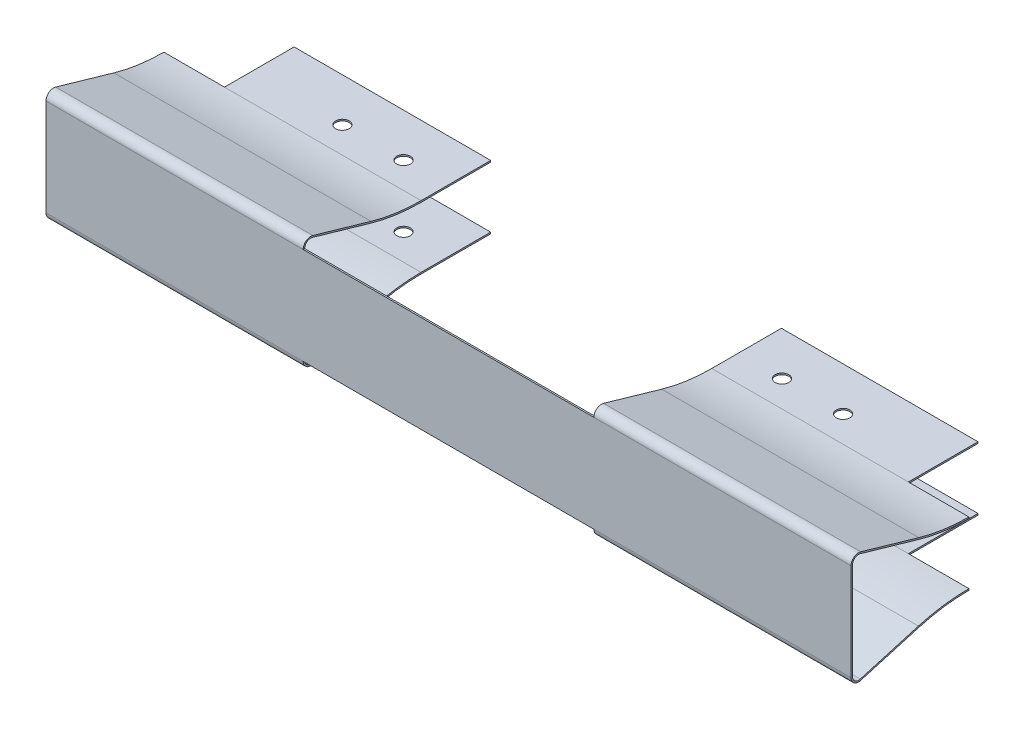
SolidWorks part; units mm, degrees
ref_plane "Front Plane" through (0, 0, 0) normal (0, 0, 1) x (1, 0, 0)
ref_plane "Top Plane" through (0, 0, 0) normal (0, 1, 0) x (1, 0, 0)
ref_plane "Right Plane" through (0, 0, 0) normal (1, 0, 0) x (0, 0, -1)
sketch "Sketch1" plane through (0, 0, 0) normal (1, 0, 0) x (0, 0, -1)
  line L0 (-14.97, 5) -> (-22.97, 5) construction
  line L1 (-24.97, 8) -> (-22.97, 8) construction
  line L2 (-24.97, 8) -> (-24.97, -8) construction
  line L3 (-24.97, -8) -> (-22.97, -8) construction
  line L4 (-14.97, 5) -> (-14.97, 3) construction
  line L5 (-24.97, 8) -> (-14.97, -5) construction
  line L6 (-24.97, -8) -> (-14.97, 5) construction
  line L7 (-22.97, 5) -> (-22.97, 8) construction
  line L8 (-14.97, 3) -> (-21.97, 3) construction
  line L9 (-21.97, 3) -> (-21.97, -3) construction
  line L10 (-21.97, -3) -> (-14.97, -3) construction
  line L11 (-14.97, -5) -> (-22.97, -5) construction
  line L12 (-22.97, -5) -> (-22.97, -8) construction
  line L13 (-14.97, -3) -> (-14.97, -5) construction
  line L14 (-24.97, 8) -> (-24.97, -8)
  line L15 (-14.0876, 6.1819) -> (-23.6921, 8.9606)
  line L16 (-5.75, 5) -> (-5.75, -5) construction
  line L17 (-5.75, -5) -> (5.75, -5) construction
  line L18 (5.75, 5) -> (5.75, -5) construction
  line L19 (-5.75, 5) -> (5.75, -5) construction
  line L20 (-5.75, -5) -> (5.75, 5) construction
  line L21 (-5.75, 5) -> (5.75, 5) construction
  line L22 (-5.75, -5.25) -> (5.75, -5.25)
  line L23 (-5.75, 5) -> (5.75, 5) construction
  line L24 (-14.0181, -6.422) -> (-23.6226, -9.2008)
  line L25 (-14.0876, -6.1819) -> (-23.6921, -8.9606)
  line L26 (-5.75, -5) -> (5.75, -5)
  line L27 (-25.22, 8) -> (-25.22, -8)
  line L28 (-5.75, 5) -> (5.75, 5)
  line L29 (-14.0181, 6.422) -> (-23.6226, 9.2008)
  line L30 (-5.75, 5.25) -> (5.75, 5.25)
  line L31 (5.75, 5.25) -> (5.75, 5)
  line L32 (5.75, -5) -> (5.75, -5.25)
  arc A0 (-24.97, -8) -> (-23.6921, -8.9606) centre (-23.97, -8) ccw
  arc A1 (-23.6921, 8.9606) -> (-24.97, 8) centre (-23.97, 8) ccw
  arc A2 (-5.75, -5.25) -> (-14.0181, -6.422) centre (-5.75, -35) ccw
  arc A3 (-25.22, -8) -> (-23.6226, -9.2008) centre (-23.97, -8) ccw
  arc A4 (-23.6226, 9.2008) -> (-25.22, 8) centre (-23.97, 8) ccw
  arc A5 (-5.75, 5.25) -> (-14.0181, 6.422) centre (-5.75, 35) cw
  arc A6 (-5.75, -5) -> (-14.0876, -6.1819) centre (-5.75, -35) ccw
  arc A7 (-5.75, 5) -> (-14.0876, 6.1819) centre (-5.75, 35) cw
  point P0 (-18.8162, 0)
  point P1 (0, 0)
  dimension "D13" = 30
  dimension "D17" = 1
  dimension "D1" = 16
  dimension "D2" = 10
  dimension "D3" = 2
  dimension "D4" = 2
  dimension "D5" = 2
  dimension "D6" = 3
  dimension "D7" = 6
  dimension "D8" = 3
  dimension "D9" = 11.5
  dimension "D10" = 10
  dimension "D11" = 16.22
  dimension "D12" = 0.25
extrude "Extrude1" add sketch "Sketch1" along normal mid plane 132.92
sketch "Sketch2" plane through (0, 0, 0) normal (0, 0, 1) x (1, 0, 0)
  line L0 (-24, 8) -> (-24, 9.25)
  line L1 (-24, 8) -> (24, 8)
  line L2 (-24, 8) -> (-24, -8) construction
  line L3 (-24, -8) -> (24, -8)
  line L4 (24, 8) -> (24, -8) construction
  line L5 (-24, 8) -> (24, -8) construction
  line L6 (-24, -8) -> (24, 8) construction
  line L8 (-24, 9.25) -> (24, 9.25)
  line L9 (24, 9.25) -> (24, 8)
  line L10 (24, -8) -> (24, -9.25)
  line L12 (24, -9.25) -> (-24, -9.25)
  line L13 (-24, -9.25) -> (-24, -8)
  line L14 (66.46, 9.25) -> (-66.46, 9.25) construction
  line L15 (-66.46, -9.25) -> (66.46, -9.25) construction
  point P0 (0, 0)
  dimension "D1" = 48
  dimension "D2" = 16
extrude "Cut-Extrude1" cut sketch "Sketch2" along normal through all
sketch "Sketch3" plane through (0, 0, 0) normal (0, 1, 0) x (1, 0, 0)
  line L1 (-24, -24.97) -> (24, -24.97)
  line L2 (-24, -24.97) -> (-24, 5.75)
  line L3 (-24, 5.75) -> (24, 5.75)
  line L4 (24, -24.97) -> (24, 5.75)
  line L5 (-24, -24.97) -> (24, 5.75) construction
  line L6 (-24, 5.75) -> (24, -24.97) construction
  line L9 (24, -24.97) -> (-24, -24.97) construction
  line L11 (-24, -19.4723) -> (-24, -23.6226) construction
  line L12 (66.46, 5.75) -> (-66.46, 5.75) construction
  point P0 (0, -9.61)
extrude "Cut-Extrude2" cut sketch "Sketch3" against normal through all and the other way through all
sketch "Sketch4" plane through (0, 0, 0) normal (0, 1, 0) x (1, 0, 0)
  line L3 (0, 0) -> (0, -20.9406) construction
  line L5 (-66.46, 5.75) -> (-56.46, 5.75)
  line L6 (-66.46, 5.75) -> (-66.46, -5.75)
  line L7 (-66.46, -5.75) -> (-56.46, -5.75)
  line L8 (-56.46, 5.75) -> (-56.46, -5.75)
  line L9 (-66.46, 5.75) -> (-56.46, -5.75) construction
  line L10 (-66.46, -5.75) -> (-56.46, 5.75) construction
  line L11 (66.46, -5.75) -> (56.46, 5.75) construction
  line L12 (66.46, 5.75) -> (56.46, -5.75) construction
  line L13 (66.46, 5.75) -> (56.46, 5.75)
  line L14 (66.46, 5.75) -> (66.46, -5.75)
  line L15 (66.46, -5.75) -> (56.46, -5.75)
  line L16 (56.46, 5.75) -> (56.46, -5.75)
  line L17 (-24, 5.75) -> (-66.46, 5.75) construction
  line L18 (-24, -5.75) -> (-66.46, -5.75) construction
  line L19 (-66.46, 5.75) -> (-66.46, -5.75) construction
  circle A0 centre (-61.46, 0) radius 1.75 construction
  circle A1 centre (-41.34, -1.4) radius 1.125
  circle A2 centre (-31.24, -1.4) radius 1.125
  circle A3 centre (31.24, -1.4) radius 1.125
  circle A4 centre (41.34, -1.4) radius 1.125
  dimension "D3" = 3.5
  dimension "D4" = 2.25
  dimension "D5" = 2.25
  dimension "D1" = 5.75
  dimension "D6" = 10.1
  dimension "D7" = 20.12
  dimension "D8" = 1.4
  dimension "D9" = 10
extrude "Cut-Extrude3" cut sketch "Sketch4" against normal through all and the other way through all
